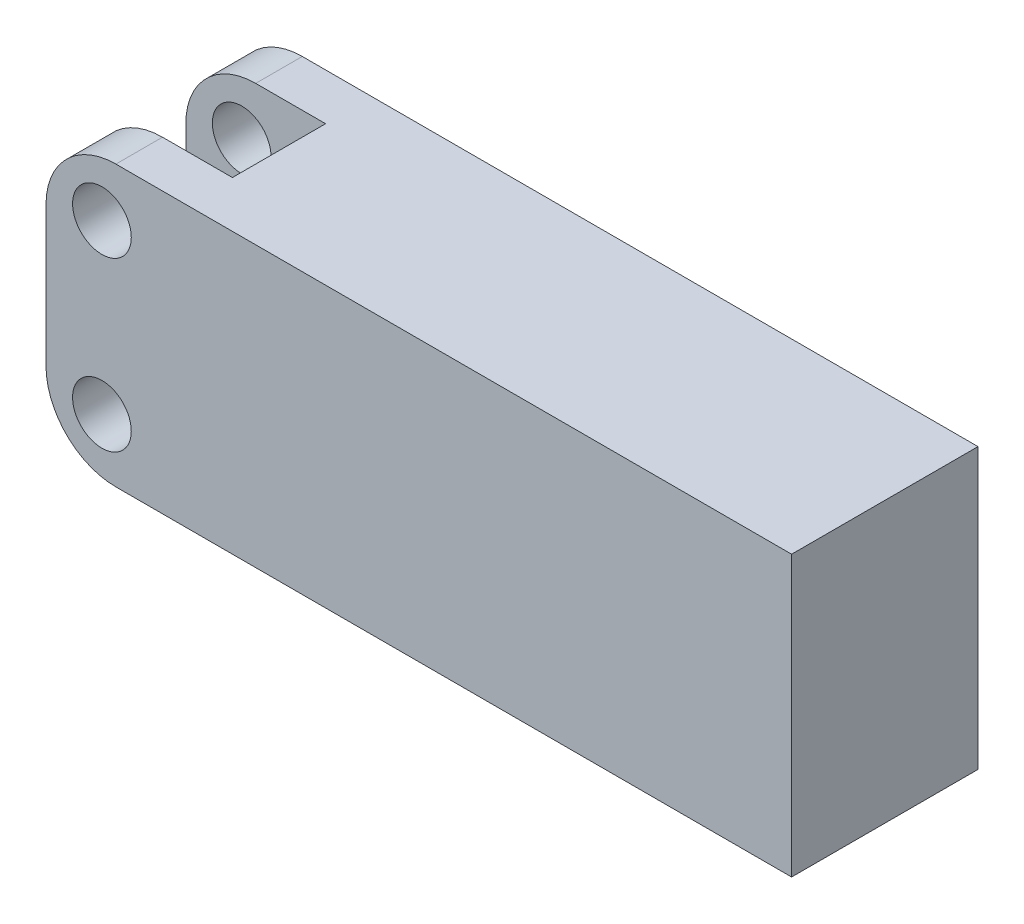
SolidWorks part; units mm, degrees
ref_plane "Front Plane" through (0, 0, 0) normal (0, 0, 1) x (1, 0, 0)
ref_plane "Top Plane" through (0, 0, 0) normal (0, 1, 0) x (1, 0, 0)
ref_plane "Right Plane" through (0, 0, 0) normal (1, 0, 0) x (0, 0, -1)
sketch "Sketch1" plane through (0, 0, 0) normal (0, 0, 1) x (1, 0, 0)
  line L1 (0, 0) -> (50.8, 0)
  line L2 (0, 0) -> (0, 19.05)
  line L3 (0, 19.05) -> (50.8, 19.05)
  line L4 (50.8, 0) -> (50.8, 19.05)
  circle A0 centre (3.81, 3.81) radius 2
  circle A1 centre (3.81, 15.24) radius 2
  point P9 (4.3395, 9.1455)
  point P10 (4.3395, 3.2688)
  point P11 (0, 0)
  point P12 (0, 0)
  dimension "D3" = 4
  dimension "D1" = 19.05
  dimension "D2" = 50.8
  dimension "D5" = 3.81
  dimension "D6" = 3.81
  dimension "D7" = 3.81
extrude "Boss-Extrude1" add sketch "Sketch1" along normal blind 12.7
sketch "Sketch2" plane through (0, 19.05, 0) normal (0, 1, 0) x (1, 0, 0)
  line L0 (5.81, 0) -> (1.81, 0) construction
  line L1 (5.81, 0) -> (1.81, 0)
  line L2 (0, -12.7) -> (0, 0) construction
  line L3 (0, -3.175) -> (9.525, -3.175)
  line L4 (0, -3.175) -> (0, -9.525)
  line L5 (0, -9.525) -> (9.525, -9.525)
  line L6 (9.525, -3.175) -> (9.525, -9.525)
  point P2 (3.81, 0)
  point P9 (0, -6.35)
  point P10 (0, 0)
  point P11 (0, 0)
  line M6 (0, 0) -> (0, -12.7)
  dimension "D1" = 9.525
  dimension "D2" = 6.35
extrude "Cut-Extrude1" cut sketch "Sketch2" against normal blind 10.5 contours L6 L3 L5 M6
fillet "Fillet1" radius 4.7625 1 edges at (9.525, 8.55, 6.35)
fillet "Fillet2" radius 4.7625 3 edges at (0, 19.05, 11.1125) (0, 19.05, 1.5875) (0, 0, 6.35)
ref_plane "Plane1" through (0, 0, 6.35) normal (0, 0, -1) x (-1, 0, 0)
equation "\"D7@Sketch1\"=\"D6@Sketch1\""
